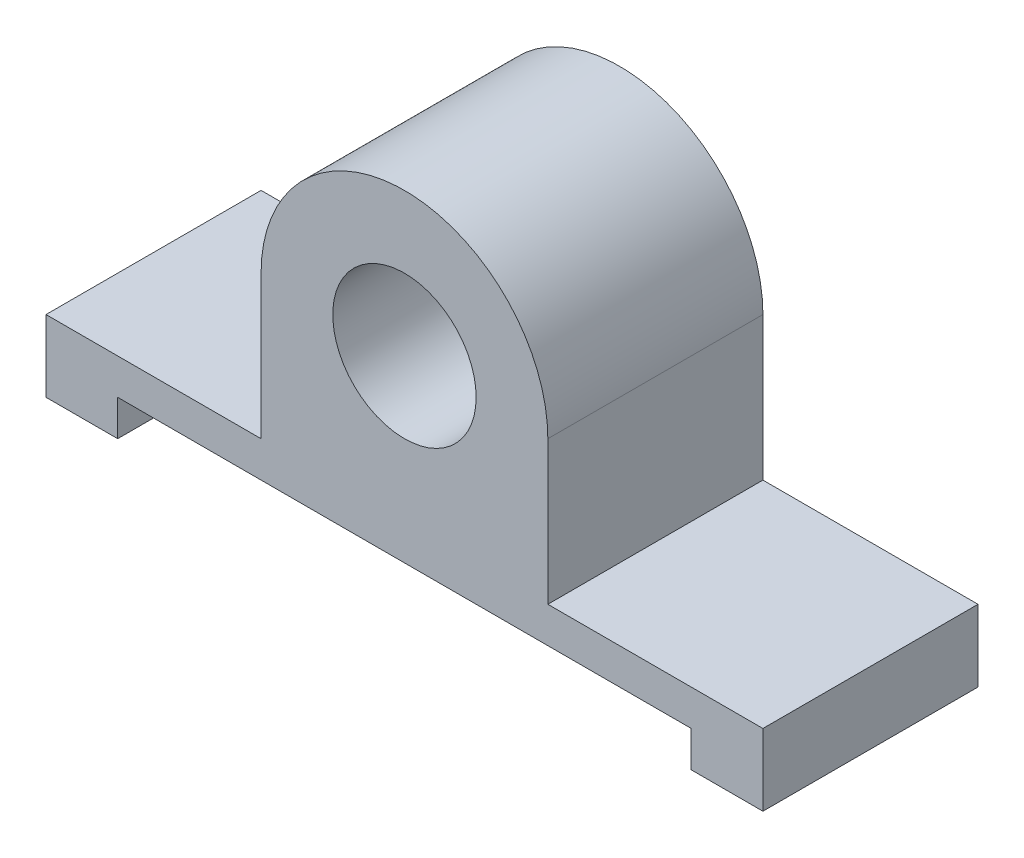
SolidWorks part; units mm, degrees
ref_plane "Front Plane" through (0, 0, 0) normal (0, 0, 1) x (1, 0, 0)
ref_plane "Top Plane" through (0, 0, 0) normal (0, 1, 0) x (1, 0, 0)
ref_plane "Right Plane" through (0, 0, 0) normal (1, 0, 0) x (0, 0, -1)
sketch "Sketch1" plane through (0, 0, 0) normal (0, 0, 1) x (1, 0, 0)
  line L0 (1.8748, -21.7468) -> (1.8748, -42.915) construction
  line L1 (-38.1252, -20.7557) -> (41.8748, -20.7557)
  line L2 (41.8748, -20.7557) -> (41.8748, -25.7557)
  line L3 (41.8748, -25.7557) -> (51.8748, -25.7557)
  line L4 (51.8748, -25.7557) -> (51.8748, -15.7557)
  line L5 (51.8748, -15.7557) -> (21.8748, -15.7557)
  line L6 (21.8748, 4.2443) -> (21.8748, -15.7557)
  line L7 (-18.1252, 4.2443) -> (-18.1252, -15.7557)
  line L8 (-48.1252, -15.7557) -> (-18.1252, -15.7557)
  line L9 (-48.1252, -25.7557) -> (-48.1252, -15.7557)
  line L10 (-38.1252, -25.7557) -> (-48.1252, -25.7557)
  line L11 (-38.1252, -20.7557) -> (-38.1252, -25.7557)
  circle A0 centre (1.8748, 4.2443) radius 10
  arc A1 (21.8748, 4.2443) -> (-18.1252, 4.2443) centre (1.8748, 4.2443) ccw
  point P9 (1.8748, -20.7557)
  point P16 (20.9846, -13.5474)
  point P20 (1.8748, -20.7557)
  dimension "D1" = 40
  dimension "D2" = 20
  dimension "D3" = 20
  dimension "D4" = 10
  dimension "D5" = 5
  dimension "D6" = 10
  dimension "D7" = 80
extrude "Boss-Extrude1" add sketch "Sketch1" along normal blind 30
